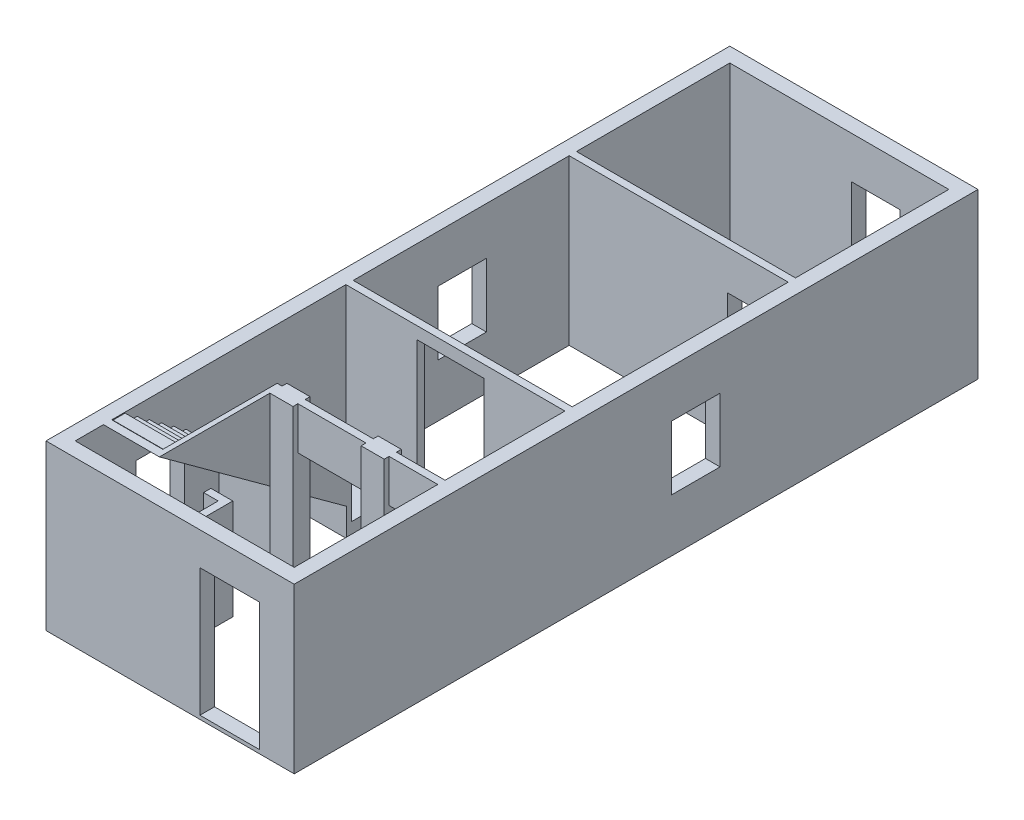
SolidWorks part; units mm, degrees
material "屋面瓦"
ref_plane "前视基准面" through (0, 0, 0) normal (0, 0, 1) x (1, 0, 0)
ref_plane "上视基准面" through (0, 0, 0) normal (0, 1, 0) x (1, 0, 0)
ref_plane "右视基准面" through (0, 0, 0) normal (1, 0, 0) x (0, 0, -1)
sketch "草图1" plane through (0, 0, 0) normal (0, 1, 0) x (1, 0, 0)
  line L1 (0, 0) -> (-3600, 0)
  line L2 (0, 0) -> (0, 10760)
  line L3 (0, 10760) -> (-3600, 10760)
  line L4 (-3600, 0) -> (-3600, 10760)
  point P4 (-1800, 0)
  dimension "D1" = 10760
  dimension "D2" = 3600
extrude "墙" add sketch "草图1" along normal blind 2700 thin thin type one direction wall 240
ref_plane "中间面-宽向" through (-1800, 0, 0) normal (1, 0, 0) x (0, 0, -1)
sketch "草图6" plane through (0, 0, 0) normal (0, 1, 0) x (1, 0, 0)
  line L0 (-3600, 8240) -> (0, 8240)
  line L4 (-3600, 10760) -> (-3600, 0) construction
  line L5 (0, 0) -> (0, 10760) construction
  line L6 (0, 10760) -> (-3600, 10760) construction
  dimension "D1" = 2520
extrude "房墙" add sketch "草图6" along normal up to surface (2700 mm away) thin
sketch "草图12" plane through (0, 0, 0) normal (0, 1, 0) x (1, 0, 0)
  line L0 (-1000, 8360) -> (-1000, 8240) construction
  line L1 (0, 8240) -> (-1240, 8240)
  line L2 (0, 8240) -> (0, 8360)
  line L3 (0, 8360) -> (-1240, 8360)
  line L4 (-1240, 8240) -> (-1240, 8360)
  line L5 (-200, 8360) -> (-200, 8240) construction
  dimension "D1" = 200
  dimension "D2" = 120
  dimension "D3" = 240
  dimension "D4" = 800
extrude "房门框" add sketch "草图12" along normal blind 2220
sketch "草图10" plane through (0, 0, -8120) normal (0, 0, 1) x (1, 0, 0)
  line L0 (-3600, 0) -> (0, 0) construction
  line L1 (-1000, 2050) -> (-200, 2050)
  line L2 (-1000, 2050) -> (-1000, 0)
  line L3 (-1000, 0) -> (-200, 0)
  line L4 (-200, 2050) -> (-200, 0)
  dimension "D1" = 2050
extrude "房门" cut sketch "草图10" against normal up to next
sketch "草图7" plane through (0, 0, 0) normal (0, 1, 0) x (1, 0, 0)
  line L0 (-3600, 4570) -> (0, 4570)
  line L1 (-3600, 8120) -> (-3600, 0) construction
  line L2 (0, 0) -> (0, 8120) construction
  line L3 (-3600, 8120) -> (0, 8120) construction
  dimension "D1" = 3550
extrude "大门墙" add sketch "草图7" along normal up to surface (2700 mm away) thin
sketch "草图13" plane through (0, 0, -4450) normal (0, 0, 1) x (1, 0, 0)
  line L1 (-2430, 2500) -> (-1330, 2500)
  line L2 (-2430, 2500) -> (-2430, 100)
  line L3 (-2430, 100) -> (-1330, 100)
  line L4 (-1330, 2500) -> (-1330, 100)
  line L6 (-3840, 0) -> (240, 0) construction
  dimension "D1" = 2400
  dimension "D2" = 100
  dimension "D3" = 1100
  dimension "D4" = 1330
extrude "大门" cut sketch "草图13" against normal up to next
sketch "草图8" plane through (0, 0, 0) normal (0, 1, 0) x (1, 0, 0)
  line L0 (-3600, 2480) -> (0, 2480)
  line L1 (-3600, 4450) -> (-3600, 0) construction
  line L2 (0, 0) -> (0, 4450) construction
  line L3 (-3600, 4450) -> (0, 4450) construction
  dimension "D1" = 1970
extrude "天井墙" add sketch "草图8" along normal up to surface (2700 mm away) thin
sketch "草图17" plane through (-3600, 0, 0) normal (1, 0, 0) x (0, 0, -1)
  line L0 (464.1323, 2700) -> (3540, 459.3017)
  line L1 (4450, 2700) -> (4450, 0) construction
  line L2 (3540, 459.3017) -> (3540, 0)
  line L3 (0, 0) -> (10760, 0) construction
  line L4 (3540, 0) -> (3620, 0)
  line L5 (3620, 0) -> (3620, 500)
  line L6 (3620, 500) -> (600, 2700)
  line L7 (-240, 2700) -> (11000, 2700) construction
  line L8 (0, 2700) -> (0, 0) construction
  line L9 (464.1323, 2700) -> (600, 2700)
  dimension "D1" = 80
  dimension "D2" = 80
  dimension "D3" = 500
  dimension "D4" = 600
  dimension "D5" = 830
extrude "梯面" add sketch "草图17" along normal blind 840
sketch "草图18" plane through (-2760, 0, 0) normal (1, 0, 0) x (0, 0, -1)
  line L2 (464.1323, 2700) -> (3540, 459.3017)
  line L3 (464.1323, 2700) -> (2480, 2700)
  line L5 (-240, 2700) -> (11000, 2700) construction
  line L6 (464.1323, 2700) -> (2360, 1318.9043) construction
  line L7 (2480, 2250.4636) -> (3620, 1420)
  line L8 (3620, 1420) -> (3620, 0)
  line L9 (3620, 0) -> (3620, 500) construction
  line L10 (0, 0) -> (10760, 0) construction
  line L11 (2480, 2250.4636) -> (2480, 2700)
  line L12 (2480, 2700) -> (2480, 0) construction
  line L13 (3540, 0) -> (3620, 0)
  line L14 (3540, 0) -> (3540, 459.3017)
  line L15 (3540, 459.3017) -> (3540, 0) construction
  dimension "D1" = 1420
extrude "梯墙" add sketch "草图18" along normal blind 80
sketch "草图19" plane through (0, 2700, 0) normal (0, 1, 0) x (1, 0, 0)
  line L0 (-3600, 0) -> (-3600, 10760) construction
  line L1 (-3600, 2480) -> (-2760, 2480)
  line L2 (-3600, 2480) -> (-3600, 2360)
  line L3 (-3600, 2360) -> (-2760, 2360)
  line L4 (-2760, 2480) -> (-2760, 2360)
  line L5 (-2760, 3620) -> (-2760, 2480) construction
  line L6 (-3600, 2480) -> (0, 2480) construction
  line L7 (-3600, 2360) -> (-2760, 2360) construction
extrude "切除-梯隔墙" cut sketch "草图19" against normal up to surface (1369.5364 mm away)
sketch "草图20" plane through (0, 0, 0) normal (0, 1, 0) x (1, 0, 0)
  line L0 (-2860, 1490) -> (-2500, 1490)
  line L1 (-2500, 1490) -> (-2500, 0)
  line L2 (0, 0) -> (-3600, 0) construction
  line L3 (-3600, 0) -> (-3600, 10760) construction
  dimension "D1" = 1490
  dimension "D2" = 360
  dimension "D3" = 740
extrude "厕所墙" add sketch "草图20" along normal blind 1650 thin
sketch "草图21" plane through (-3600, 0, 0) normal (1, 0, 0) x (0, 0, -1)
  line L0 (3620, 500) -> (3620, 645.6954)
  line L2 (3620, 645.6954) -> (3420, 645.6954)
  line L3 (3620, 500) -> (600, 2700) construction
  line L4 (3420, 645.6954) -> (3620, 500)
  line L5 (3620, 0) -> (3620, 1420) construction
  dimension "D1" = 36.072
  dimension "D2" = 200
  dimension "D3" = 247.4412
extrude "梯" add sketch "草图21" along normal up to next (840 mm away)
pattern_linear "阵列梯" count 15 spacing 247.44 along (0, 1, 0) of "梯"
sketch "草图22" plane through (0, 0, 0) normal (0, 1, 0) x (1, 0, 0)
  line L0 (-2760, 3620) -> (-3600, 3620) construction
  line L1 (-3600, 4450) -> (-2680, 4450)
  line L2 (-3600, 4450) -> (-3600, 3620)
  line L3 (-3600, 3620) -> (-2680, 3620)
  line L4 (-2680, 4450) -> (-2680, 3620)
  line L5 (-2680, 3620) -> (-2680, 2480) construction
extrude "凸台-拉伸7" add sketch "草图22" along normal blind 200
sketch "草图23" plane through (0, 200, 0) normal (0, 1, 0) x (1, 0, 0)
  line L0 (-3600, 4450) -> (-3600, 3620)
  line L1 (-3600, 4450) -> (-3600, 600) construction
  line L2 (-2760, 3620) -> (-3600, 3620) construction
  line L3 (-3600, 3620) -> (-2680, 3620)
  line L4 (-2680, 3620) -> (-3600, 4450)
extrude "凸台-拉伸8" add sketch "草图23" along normal blind 200
sketch "草图14" plane through (0, 0, 0) normal (0, 1, 0) x (1, 0, 0)
  line L0 (-990, 2480) -> (-990, 2360) construction
  line L1 (-1180, 2560) -> (-800, 2560)
  line L2 (-1180, 2560) -> (-1180, 2280)
  line L3 (-1180, 2280) -> (-800, 2280)
  line L4 (-800, 2560) -> (-800, 2280)
  line L5 (-1180, 2560) -> (-800, 2280) construction
  line L6 (-1180, 2280) -> (-800, 2560) construction
  line L7 (-2680, 2560) -> (-2300, 2560)
  line L8 (-2680, 2560) -> (-2680, 2280)
  line L9 (-2680, 2280) -> (-2300, 2280)
  line L10 (-2300, 2560) -> (-2300, 2280)
  line L11 (-2680, 2560) -> (-2300, 2280) construction
  line L12 (-2680, 2280) -> (-2300, 2560) construction
  line L15 (0, 0) -> (0, 2360) construction
  line L16 (-2680, 2360) -> (0, 2360) construction
  line L17 (-2760, 2480) -> (0, 2480) construction
  point P0 (-990, 2420)
  point P5 (-2490, 2420)
  dimension "D1" = 280
  dimension "D2" = 380
  dimension "D3" = 1120
  dimension "D4" = 800
extrude "天井柱" add sketch "草图14" along normal up to surface (2700 mm away)
sketch "草图15" plane through (0, 0, -2360) normal (0, 0, 1) x (1, 0, 0)
  line L4 (-800, 2700) -> (-800, 0)
  line L5 (-800, 0) -> (0, 0)
  line L6 (0, 0) -> (0, 2700)
  line L7 (0, 2700) -> (-800, 2700)
  line L8 (-800, 2000) -> (-800, 0)
  line L9 (-800, 0) -> (0, 0)
  line L10 (0, 0) -> (0, 2000)
  line L11 (0, 2000) -> (-800, 2000)
  line L12 (-2300, 2700) -> (-2300, 0)
  line L13 (-2300, 0) -> (-1180, 0)
  line L14 (-1180, 0) -> (-1180, 2700)
  line L15 (-1180, 2700) -> (-2300, 2700)
  line L16 (-2300, 2000) -> (-2300, 0)
  line L17 (-2300, 0) -> (-1180, 0)
  line L18 (-1180, 0) -> (-1180, 2000)
  line L19 (-1180, 2000) -> (-2300, 2000)
  dimension "D2" = 2000
  dimension "D1" = 0
  dimension "D3" = 0
extrude "天井开墙" cut sketch "草图15" against normal up to next
sketch "草图2" plane through (0, 0, 0) normal (0, 0, -1) x (-1, 0, 0)
  line L1 (1310, 60) -> (330, 60)
  line L2 (1310, 60) -> (1310, 2160)
  line L3 (1310, 2160) -> (330, 2160)
  line L4 (330, 60) -> (330, 2160)
  line L5 (0, 2700) -> (0, 0) construction
  line L6 (3840, 0) -> (-240, 0) construction
  dimension "D1" = 330
  dimension "D2" = 980
  dimension "D3" = 2100
  dimension "D4" = 60
extrude "外门" cut sketch "草图2" against normal through all
sketch "草图4" plane through (0, 0, -10760) normal (0, 0, 1) x (1, 0, 0)
  line L1 (-1600, 2010) -> (-800, 2010)
  line L2 (-1600, 2010) -> (-1600, 960)
  line L3 (-1600, 960) -> (-800, 960)
  line L4 (-800, 2010) -> (-800, 960)
  line L5 (0, 0) -> (-3600, 0) construction
  dimension "D1" = 1050
  dimension "D2" = 800
  dimension "D3" = 800
  dimension "D4" = 960
extrude "房窗" cut sketch "草图4" against normal through all
sketch "草图3" plane through (240, 0, 0) normal (-1, 0, 0) x (0, 0, 1)
  line L1 (-6760, 1920) -> (-5960, 1920)
  line L2 (-6760, 1920) -> (-6760, 870)
  line L3 (-6760, 870) -> (-5960, 870)
  line L4 (-5960, 1920) -> (-5960, 870)
  line L5 (0, 0) -> (-4450, 0) construction
  line L6 (-4570, 2700) -> (-4570, 0) construction
  dimension "D1" = 1390
  dimension "D2" = 800
  dimension "D3" = 870
  dimension "D4" = 1050
extrude "厅窗" cut sketch "草图3" along normal up to surface (4080 mm away) up to face at (-3840, 1350, -5380)
sketch "草图16" plane through (-3600, 0, 0) normal (1, 0, 0) x (0, 0, -1)
  line L0 (0, 2700) -> (0, 0) construction
  line L1 (1000, 1920) -> (1800, 1920)
  line L2 (1000, 1920) -> (1000, 870)
  line L3 (1000, 870) -> (1800, 870)
  line L4 (1800, 1920) -> (1800, 870)
  line L5 (1000, 1920) -> (1800, 870) construction
  line L6 (1000, 870) -> (1800, 1920) construction
  line L7 (0, 0) -> (10760, 0) construction
  point P0 (1400, 1395)
  dimension "D1" = 800
  dimension "D2" = 1050
  dimension "D3" = 1000
  dimension "D4" = 870
extrude "厕所窗" cut sketch "草图16" against normal up to next
